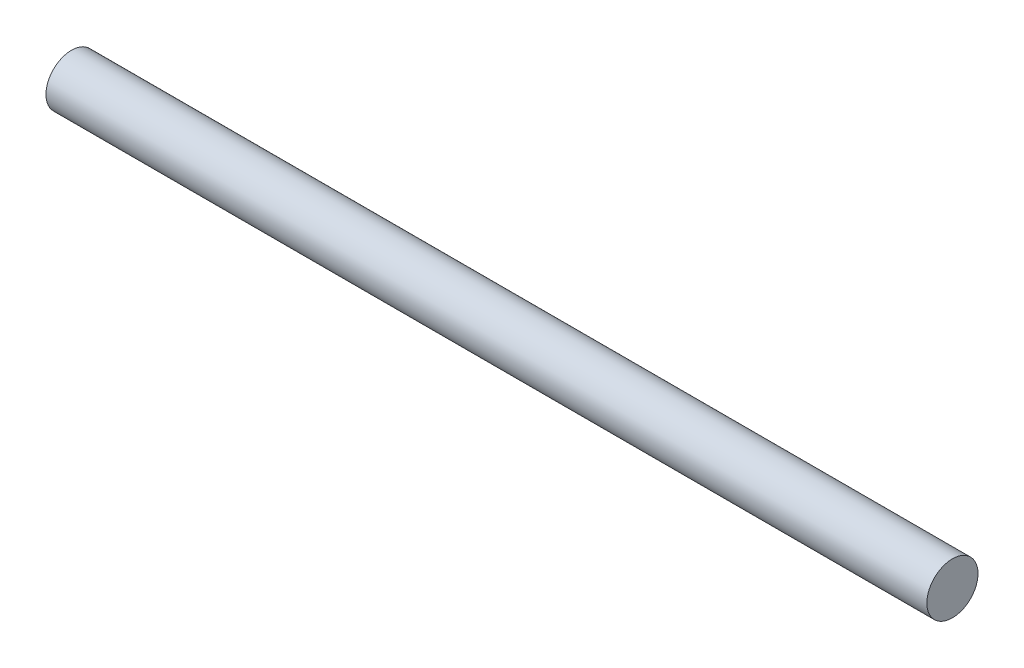
SolidWorks part; units mm, degrees
ref_plane "Plan de face" through (0, 0, 0) normal (0, 0, 1) x (1, 0, 0)
ref_plane "Plan de dessus" through (0, 0, 0) normal (0, 1, 0) x (1, 0, 0)
ref_plane "Plan de droite" through (0, 0, 0) normal (1, 0, 0) x (0, 0, -1)
sketch "Esquisse5" plane through (0, 0, 0) normal (1, 0, 0) x (0, 0, -1)
  circle A0 centre (0, 0) radius 18
extrude "Boss.-Extru.3" add sketch "Esquisse5" along normal blind 620
ref_plane "Plan2" through (10, 0, 0) normal (-1, 0, 0) x (0, 0, 1)
ref_plane "Plan4" through (610, 0, 0) normal (-1, 0, 0) x (0, 0, 1)
sketch "Esquisse6" plane through (10, 0, 0) normal (-1, 0, 0) x (0, 0, 1)
  circle A0 centre (0, 0) radius 18
sketch "Esquisse7" plane through (610, 0, 0) normal (-1, 0, 0) x (0, 0, 1)
  circle A0 centre (0, 0) radius 18
ref_plane "Plan65" through (550, 0, 0) normal (-1, 0, 0) x (0, 0, 1)
ref_plane "Plan66" through (70, 0, 0) normal (-1, 0, 0) x (0, 0, 1)
sketch "Esquisse68" plane through (550, 0, 0) normal (-1, 0, 0) x (0, 0, 1)
  circle A0 centre (0, 0) radius 18
sketch "Esquisse69" plane through (70, 0, 0) normal (-1, 0, 0) x (0, 0, 1)
  circle A0 centre (0, 0) radius 18
